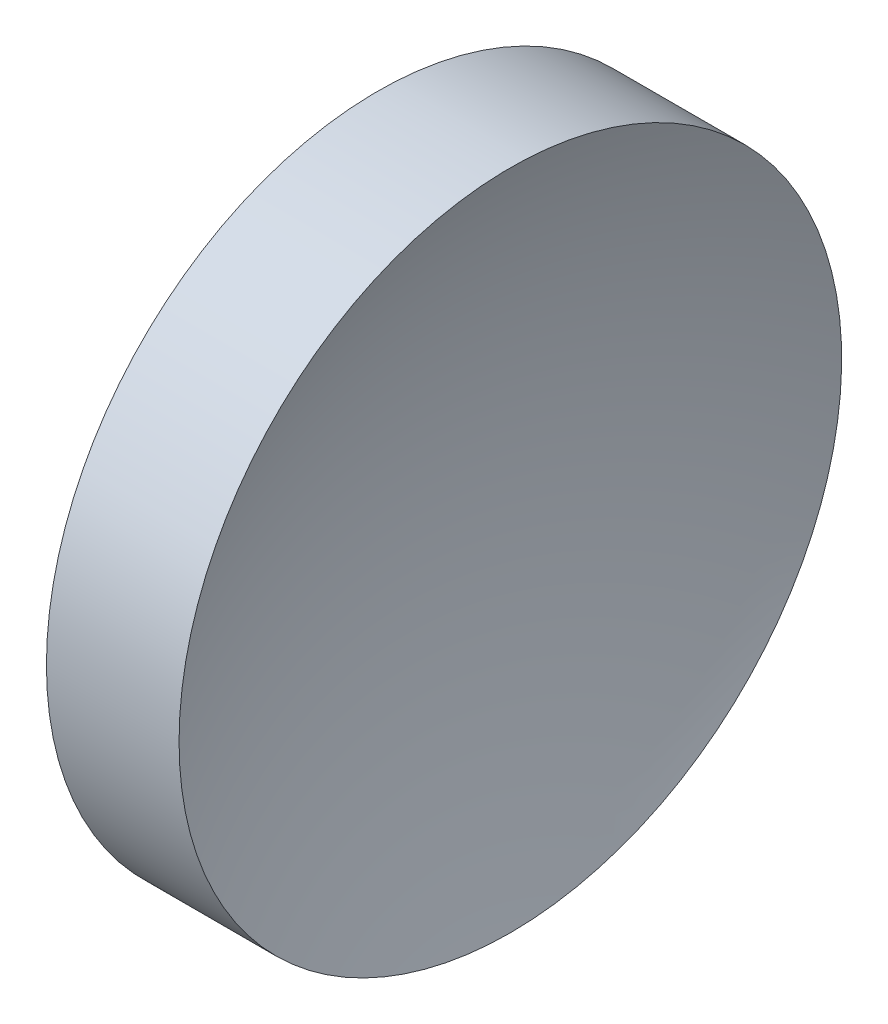
SolidWorks part; units mm, degrees
ref_plane "前视基准面" through (0, 0, 0) normal (0, 0, 1) x (1, 0, 0)
ref_plane "上视基准面" through (0, 0, 0) normal (0, 1, 0) x (1, 0, 0)
ref_plane "右视基准面" through (0, 0, 0) normal (1, 0, 0) x (0, 0, -1)
sketch "草图1" plane through (0, 0, 0) normal (0, 0, 1) x (1, 0, 0)
  line L0 (111.9552, 71.194) -> (137.836, 71.194) construction
  line L1 (119.5068, 71.194) -> (119.5068, 83.894)
  line L2 (119.5068, 83.894) -> (124.591, 83.894)
  line L3 (122.0068, 71.194) -> (119.5068, 71.194)
  arc A0 (124.591, 83.894) -> (122.0068, 71.194) centre (154.5068, 71.194) ccw
revolve "旋转1" add sketch "草图1" angle 360 about L0
